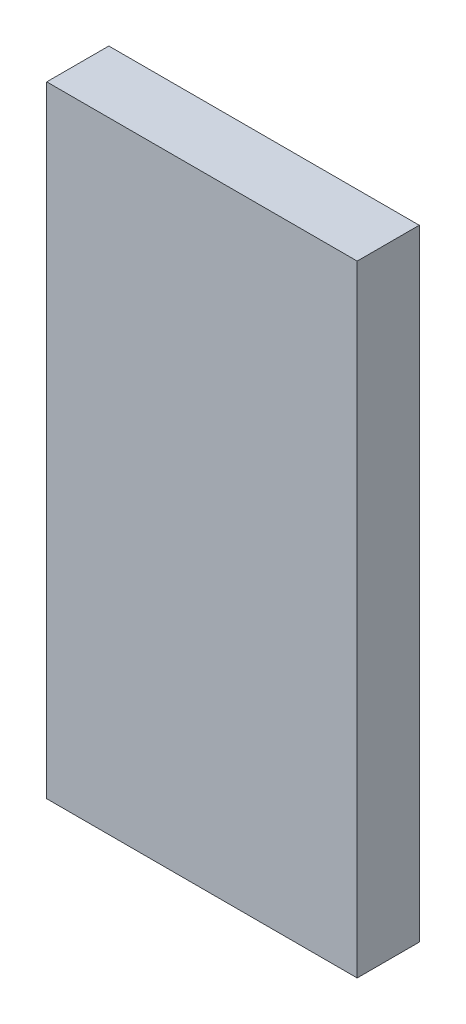
SolidWorks part; units mm, degrees
ref_plane "Přední rovina" through (0, 0, 0) normal (0, 0, 1) x (1, 0, 0)
ref_plane "Vrchní rovina" through (0, 0, 0) normal (0, 1, 0) x (1, 0, 0)
ref_plane "Pravá rovina" through (0, 0, 0) normal (1, 0, 0) x (0, 0, -1)
sketch "Skica1" plane through (0, 0, 0) normal (0, 0, 1) x (1, 0, 0)
  line L1 (-25, 50) -> (25, 50)
  line L2 (-25, 50) -> (-25, -50)
  line L3 (-25, -50) -> (25, -50)
  line L4 (25, 50) -> (25, -50)
  line L5 (-25, 50) -> (25, -50) construction
  line L6 (-25, -50) -> (25, 50) construction
  point P0 (0, 0)
  dimension "D1" = 50
  dimension "D2" = 100
extrude "Přidat vysunutím1" add sketch "Skica1" along normal blind 10
